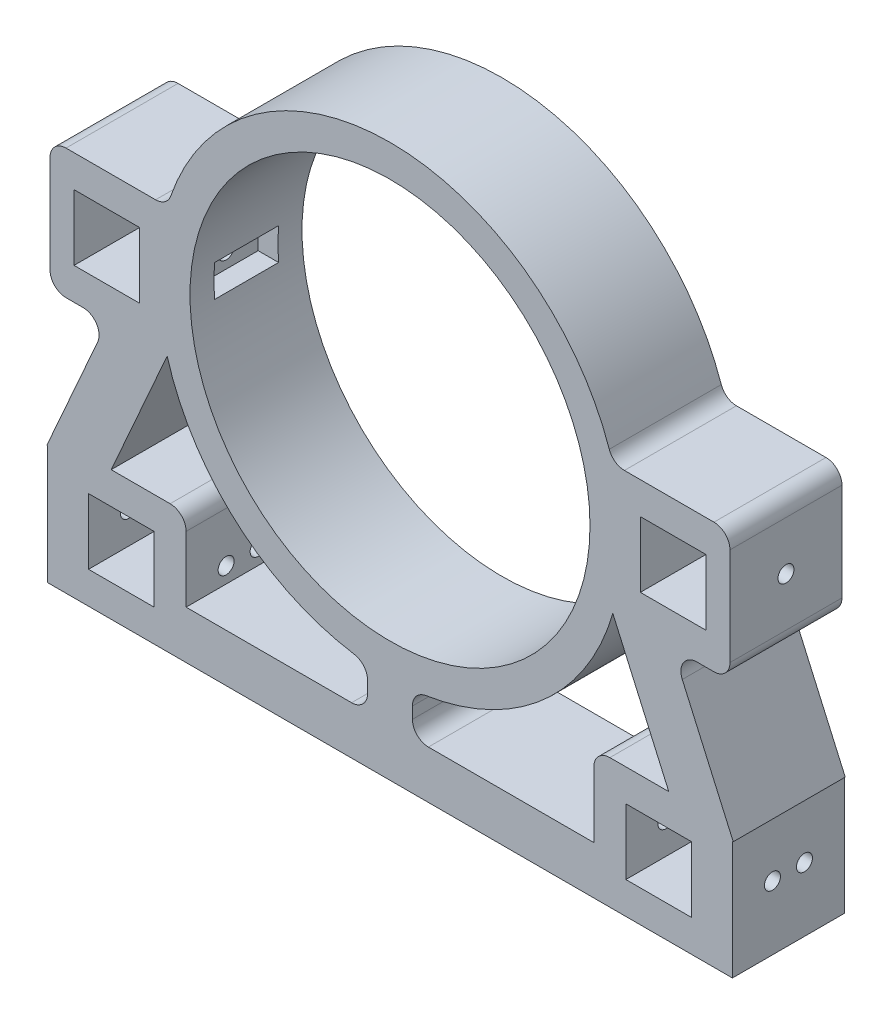
SolidWorks part; units mm, degrees
material "1023 Carbon Steel Sheet (SS)"
ref_plane "Ön Düzlem" through (0, 0, 0) normal (0, 0, 1) x (1, 0, 0)
ref_plane "Üst Düzlem" through (0, 0, 0) normal (0, 1, 0) x (1, 0, 0)
ref_plane "Sağ Düzlem" through (0, 0, 0) normal (1, 0, 0) x (0, 0, -1)
sketch "Sketch1" plane through (0, 0, 0) normal (0, 0, 1) x (1, 0, 0)
  line L0 (-7, -72.1613) -> (-7, -85.1613)
  line L1 (-7, -85.1613) -> (7, -85.1613)
  line L2 (94.2084, -90.1613) -> (73.7084, -69.6613) construction
  line L3 (94.2084, -69.6613) -> (73.7084, -90.1613) construction
  line L4 (-7, -85.1613) -> (-117, -85.1613)
  line L6 (-117, -85.1613) -> (-117, -100.1613)
  line L8 (-117, -100.1613) -> (117, -100.1613)
  line L13 (0, -100.1613) -> (0, -85.1613)
  line L14 (63.7084, -85.1613) -> (63.7084, -59.6613)
  line L15 (63.7084, -59.6613) -> (105.7084, -59.6613)
  line L16 (94.2084, -69.6613) -> (73.7084, -69.6613)
  line L17 (-117, -85.1613) -> (-66.2915, 29.3544)
  line L20 (-63.7084, -85.1613) -> (-63.7084, -59.6613)
  line L21 (-63.7084, -59.6613) -> (-105.7084, -59.6613)
  line L22 (-92.6994, -72.2698) -> (-69.6344, -20.1817)
  line L23 (94.2084, -90.1613) -> (94.2084, -69.6613)
  line L28 (-69.6344, -20.1817) -> (-108.7348, -20.1817)
  line L29 (-94.2084, -90.1613) -> (-73.7084, -90.1613)
  line L30 (94.2084, -90.1613) -> (73.7084, -90.1613)
  line L31 (73.7084, -90.1613) -> (73.7084, -69.6613)
  line L32 (7, -85.1613) -> (117, -85.1613)
  line L37 (7, -72.1613) -> (7, -85.1613)
  line L38 (117, -85.1613) -> (117, -100.1613)
  line L39 (-94.2084, -90.1613) -> (-94.2084, -69.6613)
  line L40 (-94.2084, -69.6613) -> (-73.7084, -69.6613)
  line L41 (-73.7084, -90.1613) -> (-73.7084, -69.6613)
  line L42 (-94.2084, -90.1613) -> (-73.7084, -69.6613) construction
  line L43 (-94.2084, -69.6613) -> (-73.7084, -90.1613) construction
  line L44 (-108.7348, -20.1817) -> (-108.7348, 20.3183)
  line L45 (-108.7348, 20.3183) -> (-69.5947, 20.3183)
  line L46 (0, -55) -> (0, 55) construction
  line L47 (-98.7348, -10.1817) -> (-78.2348, -10.1817)
  line L48 (-98.7348, -10.1817) -> (-98.7348, 10.3183)
  line L49 (-98.7348, 10.3183) -> (-78.2348, 10.3183)
  line L50 (-78.2348, -10.1817) -> (-78.2348, 10.3183)
  line L51 (-98.7348, -10.1817) -> (-78.2348, 10.3183) construction
  line L52 (-98.7348, 10.3183) -> (-78.2348, -10.1817) construction
  line L53 (98.7348, -10.1817) -> (78.2348, 10.3183) construction
  line L54 (98.7348, 10.3183) -> (78.2348, -10.1817) construction
  line L55 (108.7348, 20.3183) -> (69.5947, 20.3183)
  line L56 (108.7348, -20.1817) -> (108.7348, 20.3183)
  line L57 (98.7348, -10.1817) -> (98.7348, 10.3183)
  line L58 (69.6344, -20.1817) -> (108.7348, -20.1817)
  line L59 (78.2348, -10.1817) -> (78.2348, 10.3183)
  line L60 (78.2348, 10.3183) -> (98.7348, 10.3183)
  line L61 (98.7348, -10.1817) -> (78.2348, -10.1817)
  line L62 (117, -85.1613) -> (66.2915, 29.3544)
  line L63 (92.6994, -72.2698) -> (69.6344, -20.1817)
  circle A0 centre (0, 0) radius 62.5
  circle A1 centre (0, 0) radius 72.5
  point P9 (-94.2084, -79.9113)
  point P10 (83.9584, -79.9113)
  point P25 (-85, -85.1613)
  point P28 (-83.9584, -79.9113)
  point P38 (94.2084, -79.9113)
  point P43 (-88.4848, 0.0683)
  dimension "D1" = 125
  dimension "D2" = 10
  dimension "D6" = 10
  dimension "D7" = 17
  dimension "D11" = 20.5
  dimension "D3" = 15
  dimension "D4" = 13
  dimension "D5" = 110
  dimension "D8" = 25.5
  dimension "D9" = 10
  dimension "D10" = 20.5
  dimension "D13" = 100.1613
  dimension "D19" = 40.5
  dimension "D20" = 39.1401
  dimension "D21" = 20.5
  dimension "D22" = 20.5
  dimension "D23" = 10
  dimension "D24" = 10
  dimension "D25" = 42
ref_plane "Plane6" through (61.7, 0, 0) normal (1, 0, 0) x (0, 0, -1)
ref_plane "Plane7" through (-61.7, 0, 0) normal (1, 0, 0) x (0, 0, -1)
extrude "Boss-Extrude1" add sketch "Sketch1" along normal blind 35 contours A1 A0 | L50 L17 L45 L44 L28 L47 L48 L49 | A1 L45 L17 L50 L47 L28 | L22 L28 L17 L21 | L39 L40 L22 L21 L17 L4 | L41 L29 L39 L4 L6 L8 L13 L1 | L41 L4 L20 L21 L22 L40 | A1 L0 L1 L37 | L38 L32 L23 L30 L31 L1 L13 L8 | L16 L63 L15 L14 L32 L31 | L63 L16 L23 L32 L62 L15 | L63 L15 L62 L58 | A1 L58 L62 L61 L59 L55 | L62 L58 L56 L55 L59 L60 L57 L61
fillet "Fillet2" radius 5 10 edges at (-69.5947, 20.3183, 17.5) (-88.2265, -20.1817, 17.5) (-63.7084, -59.6613, 17.5) (7, -85.1613, 17.5) (7, -72.1613, 17.5) (-7, -85.1613, 17.5) (-7, -72.1613, 17.5) (63.7084, -59.6613, 17.5) (88.2265, -20.1817, 17.5) (69.5947, 20.3183, 17.5)
sketch "Sketch2" plane through (61.7, 0, 0) normal (1, 0, 0) x (0, 0, -1)
  line L0 (-35, -10.1817) -> (0, -10.1817) construction
  line L1 (-7.5, -4.9317) -> (-27.5, -4.9317)
  line L2 (-7.5, -4.9317) -> (-7.5, 5.0683)
  line L3 (-7.5, 5.0683) -> (-27.5, 5.0683)
  line L4 (-27.5, -4.9317) -> (-27.5, 5.0683)
  line L5 (-7.5, -4.9317) -> (-27.5, 5.0683) construction
  line L6 (-7.5, 5.0683) -> (-27.5, -4.9317) construction
  line L7 (0, -10.1817) -> (0, 10.3183) construction
  point P0 (-17.5, 0.0683)
  dimension "D1" = 20
  dimension "D2" = 10
  dimension "D3" = 5.25
  dimension "D4" = 7.5
extrude "Cut-Extrude2" cut sketch "Sketch2" along normal blind 7
sketch "Sketch3" plane through (-61.7, 0, 0) normal (1, 0, 0) x (0, 0, -1)
  line L0 (0, -10.1817) -> (0, 10.3183) construction
  line L1 (-27.5, -4.9317) -> (-7.5, -4.9317)
  line L2 (-27.5, -4.9317) -> (-27.5, 5.0683)
  line L3 (-27.5, 5.0683) -> (-7.5, 5.0683)
  line L4 (-7.5, -4.9317) -> (-7.5, 5.0683)
  line L5 (-27.5, -4.9317) -> (-7.5, 5.0683) construction
  line L6 (-27.5, 5.0683) -> (-7.5, -4.9317) construction
  line L7 (-35, -10.1817) -> (0, -10.1817) construction
  point P0 (-17.5, 0.0683)
  dimension "D1" = 20
  dimension "D2" = 10
  dimension "D3" = 7.5
  dimension "D4" = 5.25
extrude "Cut-Extrude3" cut sketch "Sketch3" against normal blind 7
sketch "Sketch4" plane through (117, 0, 0) normal (1, 0, 0) x (0, 0, -1)
  line L0 (0, -85.1613) -> (0, -27.2061) construction
  line L1 (-35, -100.1613) -> (0, -100.1613)
  line L2 (-35, -100.1613) -> (-35, -63.1613)
  line L3 (-35, -63.1613) -> (0, -63.1613)
  line L4 (0, -100.1613) -> (0, -63.1613)
  dimension "D1" = 37
extrude "Cut-Extrude4" cut sketch "Sketch4" against normal blind 10
sketch "Sketch5" plane through (-117, 0, 0) normal (-1, 0, 0) x (0, 0, 1)
  line L0 (35, -85.1613) -> (35, -27.2061) construction
  line L1 (0, -100.1613) -> (35, -100.1613)
  line L2 (0, -100.1613) -> (0, -63.1613)
  line L3 (0, -63.1613) -> (35, -63.1613)
  line L4 (35, -100.1613) -> (35, -63.1613)
  dimension "D1" = 37
extrude "Cut-Extrude5" cut sketch "Sketch5" against normal blind 10
sketch "Sketch6" plane through (108.7348, 0, 0) normal (1, 0, 0) x (0, 0, -1)
  line L5 (-35, 20.3183) -> (0, 20.3183)
  line L6 (-35, 20.3183) -> (-35, -20.1817)
  line L7 (-35, -20.1817) -> (0, -20.1817)
  line L8 (0, 20.3183) -> (0, -20.1817)
extrude "Cut-Extrude8" cut sketch "Sketch6" against normal blind 2.5
sketch "Sketch7" plane through (-108.7348, 0, 0) normal (-1, 0, 0) x (0, 0, 1)
  line L1 (0, -20.1817) -> (35, -20.1817)
  line L2 (0, -20.1817) -> (0, 20.3183)
  line L3 (0, 20.3183) -> (35, 20.3183)
  line L4 (35, -20.1817) -> (35, 20.3183)
extrude "Cut-Extrude9" cut sketch "Sketch7" against normal blind 2.5
fillet "Fillet3" radius 5 4 edges at (106.2348, -20.1817, 17.5) (106.2348, 20.3183, 17.5) (-106.2348, -20.1817, 17.5) (-106.2348, 20.3183, 17.5)
sketch "Sketch8" plane through (-68.7, 0, 0) normal (1, 0, 0) x (0, 0, -1)
  line L0 (-27.5, -4.9317) -> (-27.5, 5.0683) construction
  line L2 (-7.5, 5.0683) -> (-27.5, 5.0683) construction
  circle A0 centre (-17.5, 0.0683) radius 2.5
  dimension "D1" = 5
  dimension "D2" = 10
  dimension "D3" = 5
extrude "Cut-Extrude10" cut sketch "Sketch8" against normal blind 48 and the other way blind 194
sketch "Sketch9" plane through (-94.2084, 0, 0) normal (1, 0, 0) x (0, 0, -1)
  line L0 (-35, -63.1613) -> (-35, -100.1613) construction
  line L1 (-35, -90.1613) -> (0, -90.1613) construction
  line L2 (0, -100.1613) -> (0, -63.1613) construction
  circle A0 centre (-22.5, -80.1613) radius 2.5
  circle A1 centre (-12.5, -80.1613) radius 2.5
  dimension "D1" = 5
  dimension "D2" = 5
  dimension "D3" = 12.5
  dimension "D4" = 12.5
  dimension "D5" = 10
  dimension "D6" = 10
extrude "Cut-Extrude11" cut sketch "Sketch9" against normal blind 48 and the other way blind 48
sketch "Sketch10" plane through (94.2084, 0, 0) normal (-1, 0, 0) x (0, 0, 1)
  line L0 (0, -80.1613) -> (35, -80.1613) construction
  circle A0 centre (12.5, -80.1613) radius 2.5
  circle A1 centre (22.5, -80.1613) radius 2.5
  dimension "D1" = 5
  dimension "D2" = 10
  dimension "D3" = 5
extrude "Cut-Extrude12" cut sketch "Sketch10" against normal blind 48 and the other way blind 48
